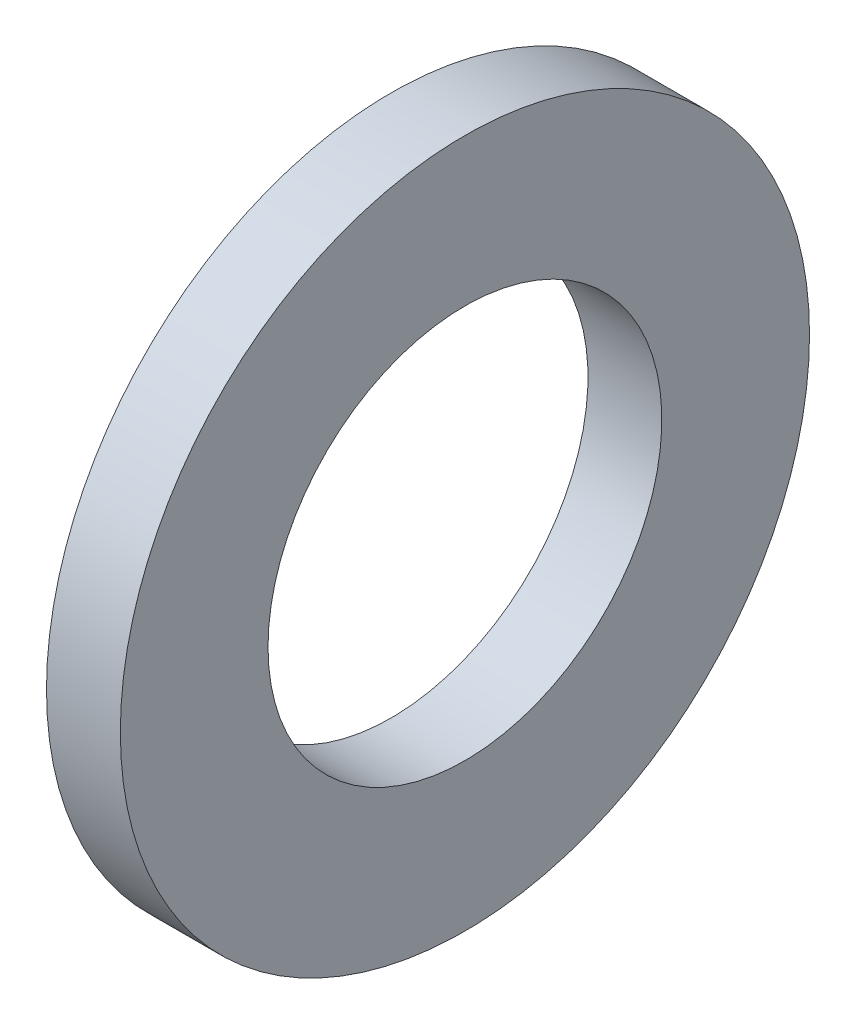
SolidWorks part; units mm, degrees
ref_plane "Face" through (0, 0, 0) normal (0, 0, 1) x (1, 0, 0)
ref_plane "Dessus" through (0, 0, 0) normal (0, 1, 0) x (1, 0, 0)
ref_plane "Droite" through (0, 0, 0) normal (1, 0, 0) x (0, 0, -1)
sketch "Esquisse1" plane through (0, 0, 0) normal (0, 0, 1) x (1, 0, 0)
  line L0 (-8.113, 34.8954) -> (-6.613, 34.8954)
  line L1 (-6.613, 34.8954) -> (-6.613, 31.8954)
  line L2 (-6.613, 31.8954) -> (-8.113, 31.8954)
  line L3 (-8.113, 31.8954) -> (-8.113, 34.8954)
  line L4 (-46.9741, 27.8954) -> (47.2752, 27.8954) construction
revolve "Révolution1" add sketch "Esquisse1" angle 360 about L4
